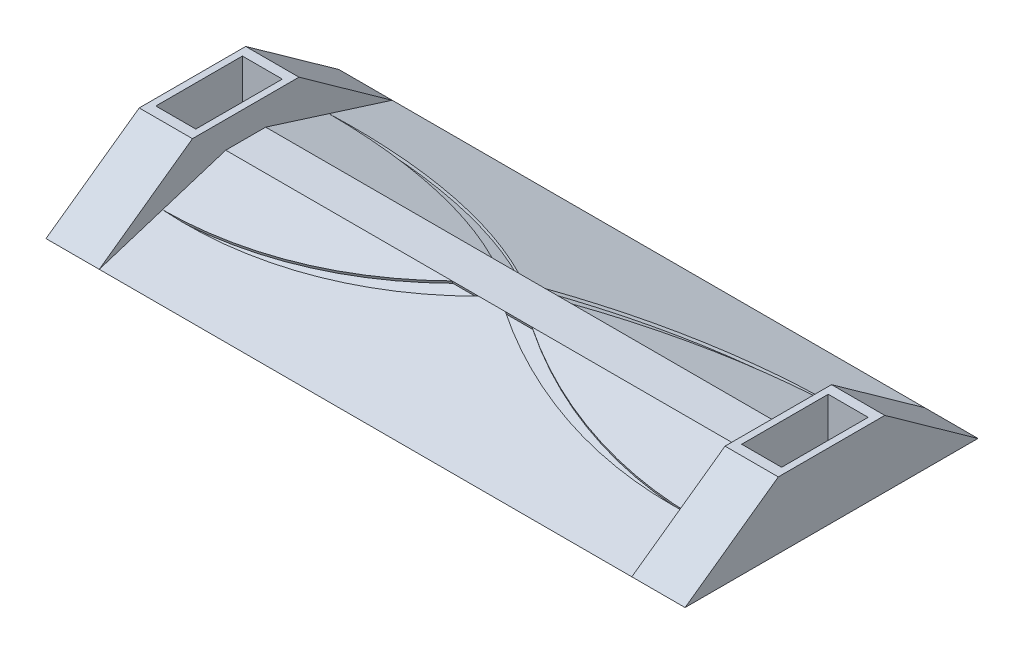
SolidWorks part; units mm, degrees
ref_plane "Front Plane" through (0, 0, 0) normal (0, 0, 1) x (1, 0, 0)
ref_plane "Top Plane" through (0, 0, 0) normal (0, 1, 0) x (1, 0, 0)
ref_plane "Right Plane" through (0, 0, 0) normal (1, 0, 0) x (0, 0, -1)
sketch "Sketch2" plane through (0, 0, 0) normal (0, 1, 0) x (1, 0, 0)
  line L1 (-100, 55) -> (100, 55)
  line L2 (-100, 55) -> (-100, -55)
  line L3 (-100, -55) -> (100, -55)
  line L4 (100, 55) -> (100, -55)
  line L5 (-100, 55) -> (100, -55) construction
  line L6 (-100, -55) -> (100, 55) construction
  point P0 (0, 0)
  dimension "D1" = 200
  dimension "D2" = 110
extrude "Boss-Extrude2" add sketch "Sketch2" along normal blind 15
sketch "Sketch3" plane through (100, 0, 0) normal (1, 0, 0) x (0, 0, -1)
  line L1 (-55, 0) -> (55, 0)
  line L2 (-55, 0) -> (-55, 25)
  line L3 (-55, 25) -> (55, 25)
  line L4 (55, 0) -> (55, 25)
  point P0 (-55, 15)
  point P1 (-55, 25)
  point P3 (55, 15)
  point P4 (55, 0)
  point P6 (55, 25)
  dimension "D1" = 10
extrude "Boss-Extrude3" add sketch "Sketch3" along normal blind 13
sketch "Sketch6" plane through (-100, 0, 0) normal (-1, 0, 0) x (0, 0, 1)
  line L0 (-55, 15) -> (55, 15) construction
  line L1 (55, 15) -> (-55, 15) construction
  line L2 (-55, 0) -> (-7.5, 15)
  line L3 (-7.5, 15) -> (-55, 15)
  line L4 (-55, 15) -> (-55, 0)
  line L5 (7.5, 15) -> (55, 0)
  line L6 (55, 0) -> (55, 15)
  line L7 (55, 15) -> (7.5, 15)
  point P0 (0, 15)
  point P1 (7.5, 15)
  point P4 (-7.5, 15)
  dimension "D1" = 7.5
  dimension "D2" = 7.5
extrude "Cut-Extrude1" cut sketch "Sketch6" against normal blind 200
sketch "Sketch8" plane through (113, 0, 0) normal (1, 0, 0) x (0, 0, -1)
  line L1 (-55, 0) -> (55, 0)
  line L2 (-55, 0) -> (-55, 25)
  line L3 (-55, 25) -> (55, 25)
  line L4 (55, 0) -> (55, 25)
extrude "Boss-Extrude5" add sketch "Sketch8" along normal blind 7
sketch "Sketch9" plane through (0, 25, 0) normal (0, 1, 0) x (1, 0, 0)
  line L0 (100, 55) -> (100, -55) construction
  line L1 (120, 55) -> (120, -55) construction
  line L3 (117.5, -16.25) -> (102.5, -16.25)
  line L4 (117.5, -16.25) -> (117.5, 16.25)
  line L5 (117.5, 16.25) -> (102.5, 16.25)
  line L6 (102.5, -16.25) -> (102.5, 16.25)
  line L7 (117.5, -16.25) -> (102.5, 16.25) construction
  line L8 (117.5, 16.25) -> (102.5, -16.25) construction
  point P0 (100, 0)
  point P1 (120, 0)
  point P4 (110, 0)
  point P7 (110, 0)
  dimension "D1" = 10
  dimension "D2" = 15
  dimension "D3" = 32.5
extrude "Cut-Extrude2" cut sketch "Sketch9" against normal blind 17.5
sketch "Sketch10" plane through (-100, 0, 0) normal (-1, 0, 0) x (0, 0, 1)
  line L1 (-55, 0) -> (55, 0)
  line L2 (-55, 0) -> (-55, 25)
  line L3 (-55, 25) -> (55, 25)
  line L4 (55, 0) -> (55, 25)
extrude "Boss-Extrude6" add sketch "Sketch10" along normal blind 20
sketch "Sketch11" plane through (0, 25, 0) normal (0, 1, 0) x (1, 0, 0)
  line L0 (-100, -55) -> (-100, 55) construction
  line L1 (-100, 55) -> (-100, 7.5) construction
  line L2 (100, 55) -> (100, -55) construction
  line L4 (-117.5, -16.25) -> (-102.5, -16.25)
  line L5 (-117.5, -16.25) -> (-117.5, 16.25)
  line L6 (-117.5, 16.25) -> (-102.5, 16.25)
  line L7 (-102.5, -16.25) -> (-102.5, 16.25)
  line L8 (-117.5, -16.25) -> (-102.5, 16.25) construction
  line L9 (-117.5, 16.25) -> (-102.5, -16.25) construction
  point P0 (-100, 0)
  point P1 (-110, 0)
  point P4 (102.5, 16.25)
  point P5 (-100, 16.25)
  point P6 (-102.5, 16.25)
  point P10 (100, 16.25)
  point P11 (-110, 0)
  dimension "D1" = 10
  dimension "D2" = 2.5
  dimension "D3" = 2.5
extrude "Cut-Extrude3" cut sketch "Sketch11" against normal blind 17.5
sketch "Sketch12" plane through (-120, 0, 0) normal (-1, 0, 0) x (0, 0, 1)
  line L0 (55, 25) -> (-55, 25) construction
  line L1 (20, 25) -> (55, 0)
  line L2 (55, 0) -> (55, 25)
  line L3 (55, 25) -> (20, 25)
  line L4 (-20, 25) -> (-55, 25)
  line L5 (-55, 25) -> (-55, 0)
  line L6 (-55, 0) -> (-20, 25)
  point P0 (0, 25)
  point P1 (-20, 25)
  point P4 (20, 25)
  dimension "D1" = 20
  dimension "D2" = 20
extrude "Cut-Extrude4" cut sketch "Sketch12" against normal blind 20
sketch "Sketch13" plane through (120, 0, 0) normal (1, 0, 0) x (0, 0, -1)
  line L0 (55, 25) -> (-55, 25) construction
  line L1 (-20, 25) -> (-55, 25)
  line L2 (-55, 25) -> (-55, 0)
  line L3 (-55, 0) -> (-20, 25)
  line L4 (20, 25) -> (55, 0)
  line L5 (55, 0) -> (55, 25)
  line L6 (55, 25) -> (20, 25)
  point P0 (0, 25)
  point P1 (-20, 25)
  point P4 (20, 25)
  dimension "D1" = 20
extrude "Cut-Extrude5" cut sketch "Sketch13" against normal blind 20
sketch "Sketch17" plane through (0, 15.7935, 4.9874) normal (0, 0.9536, 0.3011) x (1, 0, 0)
  line L0 (100, -2.6349) -> (-100, -2.6349) construction
  line L1 (-100, -2.6349) -> (-100, -52.447) construction
  line L2 (100, -2.6349) -> (100, -52.447) construction
  line L3 (-15, -2.6349) -> (-5, -2.6349)
  line L4 (5, -2.6349) -> (15, -2.6349)
  arc A0 (-100, -27.541) -> (-15, -2.6349) centre (-100.7326, 132.4573) ccw
  arc A1 (-5, -2.6349) -> (-100, -27.541) centre (-91.1176, 132.2123) cw
  arc A2 (5, -2.6349) -> (100, -27.541) centre (91.1176, 132.2123) ccw
  arc A3 (15, -2.6349) -> (100, -27.541) centre (100.7326, 132.4573) ccw
  point P0 (0, -2.6349)
  point P1 (-5, -2.6349)
  point P4 (5, -2.6349)
  point P5 (-15, -2.6349)
  point P6 (15, -2.6349)
  point P7 (-100, -27.541)
  point P8 (100, -27.541)
  dimension "D1" = 5
  dimension "D2" = 5
  dimension "D3" = 10
  dimension "D4" = 10
extrude "Cut-Extrude11" cut sketch "Sketch17" against normal blind 1
sketch "Sketch18" plane through (0, 15.7935, -4.9874) normal (0, 0.9536, -0.3011) x (1, 0, 0)
  line L0 (100, 2.6349) -> (-100, 2.6349) construction
  line L1 (100, 52.447) -> (100, 2.6349) construction
  line L2 (-100, 52.447) -> (-100, 2.6349) construction
  line L3 (15, 2.6349) -> (5, 2.6349)
  line L4 (-5, 2.6349) -> (-15, 2.6349)
  arc A0 (100, 27.541) -> (15, 2.6349) centre (100.7326, -132.4573) ccw
  arc A1 (5, 2.6349) -> (100, 27.541) centre (91.1176, -132.2123) cw
  arc A2 (-15, 2.6349) -> (-100, 27.541) centre (-100.7326, -132.4573) ccw
  arc A3 (-5, 2.6349) -> (-100, 27.541) centre (-91.1176, -132.2123) ccw
  point P0 (0, 2.6349)
  point P1 (-5, 2.6349)
  point P4 (5, 2.6349)
  point P5 (15, 2.6349)
  point P6 (-15, 2.6349)
  point P7 (100, 27.541)
  point P15 (-100, 27.541)
  dimension "D1" = 5
  dimension "D2" = 5
  dimension "D3" = 10
  dimension "D4" = 10
extrude "Cut-Extrude12" cut sketch "Sketch18" against normal blind 1
